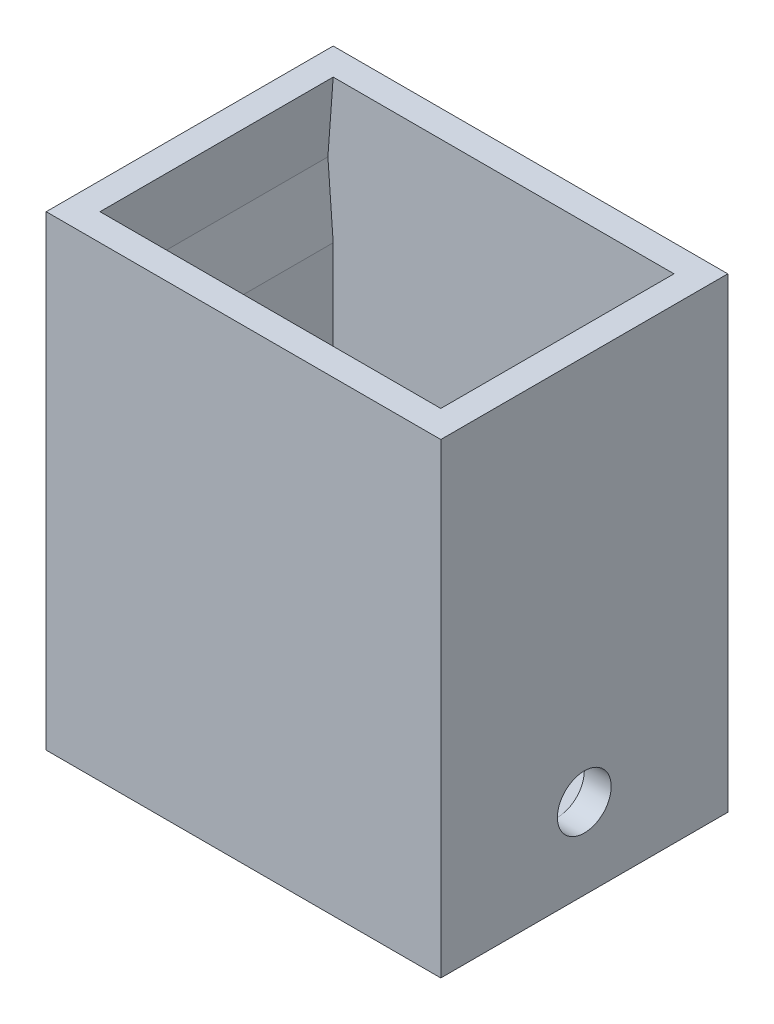
SolidWorks part; units mm, degrees
ref_plane "Спереди" through (0, 0, 0) normal (0, 0, 1) x (1, 0, 0)
ref_plane "Сверху" through (0, 0, 0) normal (0, 1, 0) x (1, 0, 0)
ref_plane "Справа" through (0, 0, 0) normal (1, 0, 0) x (0, 0, -1)
other "Configuration Table"
sketch "Эскиз1" plane through (0, 0, 0) normal (0, 1, 0) x (1, 0, 0)
  line L0 (-9.7493, 2.0735) -> (9.2507, 2.0735) construction
  line L1 (-9.7493, 8.5735) -> (9.2507, 8.5735)
  line L2 (-9.7493, 8.5735) -> (-9.7493, -4.4265)
  line L3 (-9.7493, -4.4265) -> (9.2507, -4.4265)
  line L4 (9.2507, 8.5735) -> (9.2507, -4.4265)
  line L5 (-11.2493, 10.0735) -> (10.7507, 10.0735)
  line L6 (-11.2493, 10.0735) -> (-11.2493, -5.9265)
  line L7 (-11.2493, -5.9265) -> (10.7507, -5.9265)
  line L8 (10.7507, 10.0735) -> (10.7507, -5.9265)
  line L9 (-11.2493, 2.0735) -> (10.7507, 2.0735) construction
  line L10 (-0.2493, 10.0735) -> (-0.2493, -5.9265) construction
  line L11 (-0.2493, 8.5735) -> (-0.2493, -4.4265) construction
  dimension "D1" = 19
  dimension "D2" = 13
  dimension "D3" = 22
  dimension "D4" = 16
extrude "Бобышка-Вытянуть1" add sketch "Эскиз1" along normal blind 23
sketch "Эскиз2" plane through (0, 0, 0) normal (0, -1, 0) x (1, 0, 0)
  line L1 (-11.2493, 5.9265) -> (10.7507, 5.9265)
  line L2 (-11.2493, 5.9265) -> (-11.2493, -10.0735)
  line L3 (-11.2493, -10.0735) -> (10.7507, -10.0735)
  line L4 (10.7507, 5.9265) -> (10.7507, -10.0735)
extrude "Бобышка-Вытянуть2" add sketch "Эскиз2" along normal blind 3
sketch "Эскиз3" plane through (0, 0, 0) normal (0, 1, 0) x (1, 0, 0)
  line L0 (-9.7493, 2.0735) -> (9.2507, 2.0735) construction
  line L1 (-9.7493, 8.5735) -> (-9.7493, -4.4265) construction
  line L2 (9.2507, -4.4265) -> (9.2507, 8.5735) construction
  line L3 (-0.2493, 8.5735) -> (-0.2493, -4.4265) construction
  line L4 (9.2507, 8.5735) -> (-9.7493, 8.5735) construction
  line L5 (-9.7493, -4.4265) -> (9.2507, -4.4265) construction
  circle A0 centre (-0.2493, 2.0735) radius 1.25
  dimension "D1" = 2.5
extrude "Вырез-Вытянуть1" cut sketch "Эскиз3" against normal blind 3
chamfer "Фаска1" distance 2 angle 45 1 edges at (-0.2493, 0, -0.8235)
sketch "Эскиз4" plane through (10.7507, 0, 0) normal (1, 0, 0) x (0, 0, -1)
  line L0 (-5.9265, 0) -> (10.0735, 0) construction
  line L1 (-5.9265, 23) -> (-5.9265, -3) construction
  line L2 (10.0735, 23) -> (10.0735, -3) construction
  line L3 (2.0735, 0) -> (2.0735, 23) construction
  line L4 (-5.9265, 23) -> (10.0735, 23) construction
  circle A0 centre (2.0735, 1.5) radius 1.5
  point P13 (0, 0)
  point P14 (0, 0)
  dimension "D2" = 3
  dimension "D1" = 3
  dimension "D3" = 1.5
extrude "Вырез-Вытянуть2" cut sketch "Эскиз4" against normal blind 28
sketch "Эскиз5" plane through (0, 0, -8.5735) normal (0, 0, 1) x (1, 0, 0)
  line L0 (10.7507, 19) -> (-11.2493, 19) construction
  line L1 (10.7507, 23) -> (10.7507, -3) construction
  line L2 (-11.2493, 23) -> (-11.2493, -3) construction
  line L3 (9.2507, 0) -> (9.2507, 23) construction
  line L4 (9.2507, 23) -> (-9.7493, 23) construction
  line L5 (-9.7493, 23) -> (-9.7493, 0) construction
  line L6 (-9.7493, 0) -> (9.2507, 0) construction
  line L7 (-11.2493, 15) -> (10.7507, 15) construction
  line L8 (9.2507, 23) -> (9.5451, 19)
  line L9 (9.5451, 19) -> (9.2507, 15)
  line L10 (-0.2493, 23) -> (-0.2493, 15) construction
  line L11 (-10.0438, 19) -> (-9.7493, 15)
  line L12 (-9.7493, 23) -> (-10.0438, 19)
  line L13 (-9.7493, 23) -> (-9.7493, 15)
  line L14 (9.2507, 23) -> (9.2507, 15)
  dimension "D1" = 4
  dimension "D2" = 4
extrude "Вырез-Вытянуть3" cut sketch "Эскиз5" along normal blind 13
